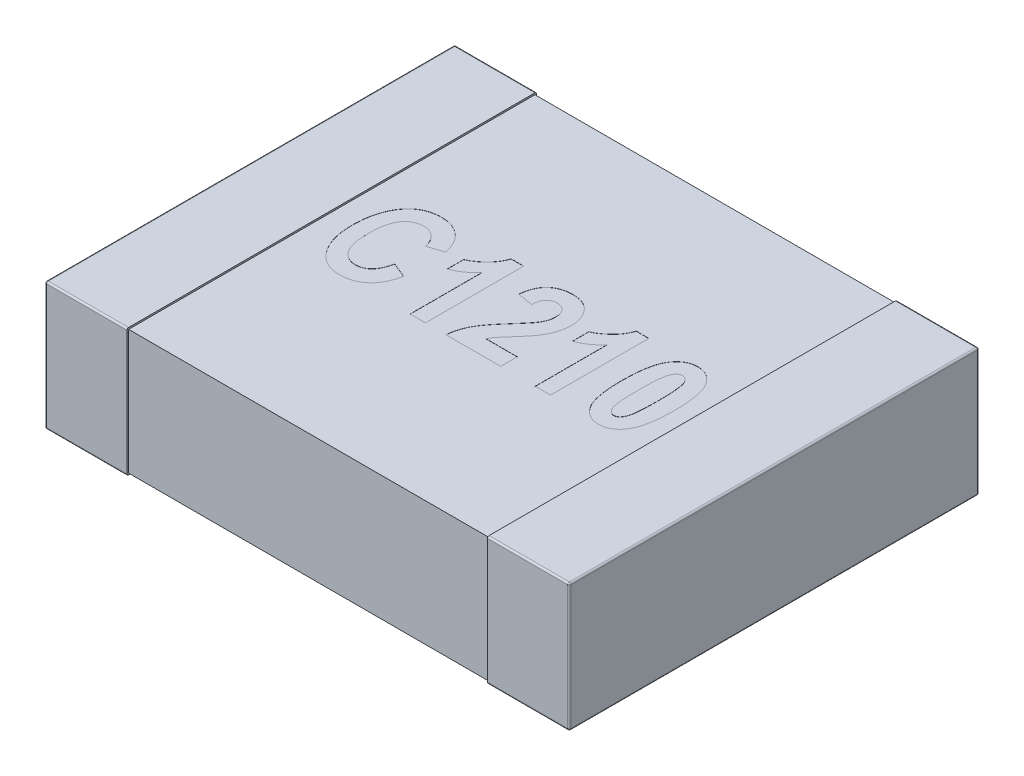
SolidWorks part; units mm, degrees
ref_plane "Front Plane" through (0, 0, 0) normal (0, 0, 1) x (1, 0, 0)
ref_plane "Top Plane" through (0, 0, 0) normal (0, 1, 0) x (1, 0, 0)
ref_plane "Right Plane" through (0, 0, 0) normal (1, 0, 0) x (0, 0, -1)
sketch "Sketch1" plane through (0, 0, 0) normal (0, 1, 0) x (1, 0, 0)
  line L0 (0, 0.15) -> (0, -0.15) construction
  line L1 (-1.6, 0) -> (0, 0) construction
  line L3 (-1.6, 1.25) -> (-1.1, 1.25)
  line L4 (-1.6, 1.25) -> (-1.6, -1.25)
  line L5 (-1.6, -1.25) -> (-1.1, -1.25)
  line L6 (-1.1, 1.25) -> (-1.1, -1.25)
  dimension "BANDWIDTH" = 0.5
  dimension "WIDTH" = 2.5
  dimension "LENGTH-HALF" = 1.6
extrude "THICKNESS" add sketch "Sketch1" along normal blind 0.78
fillet "Fillet1" radius 0.01 8 edges at (-1.6, 0, 0) (-1.35, 0, -1.25) (-1.6, 0.39, -1.25) (-1.35, 0, 1.25) (-1.6, 0.39, 1.25) (-1.6, 0.78, 0) (-1.35, 0.78, -1.25) (-1.35, 0.78, 1.25)
sketch "Sketch2" plane through (0, 0, 0) normal (1, 0, 0) x (0, 0, -1)
  line L0 (0, 0.78) -> (0, 0) construction
  line L1 (-1.24, 0.77) -> (1.24, 0.77)
  line L2 (-1.24, 0.77) -> (-1.24, 0.01)
  line L3 (-1.24, 0.01) -> (1.24, 0.01)
  line L4 (1.24, 0.77) -> (1.24, 0.01)
  line L5 (-1.24, 0.78) -> (1.24, 0.78) construction
  line L6 (-1.24, 0) -> (1.24, 0) construction
  line L7 (-1.25, 0.39) -> (1.25, 0.39) construction
  line L8 (-1.25, 0.77) -> (-1.25, 0.01) construction
  line L9 (1.25, 0.77) -> (1.25, 0.01) construction
  dimension "D1" = 0.01
  dimension "D2" = 0.01
extrude "Boss-Extrude2" add sketch "Sketch2" against normal up to surface (1.1 mm away) up to face at (-1.1, 0.39, 0)
mirror "Mirror3" about plane through (0, 0, 0) normal (1, 0, 0) of "Boss-Extrude2", "Fillet1", "THICKNESS"
sketch "Sketch3" plane through (0, 0.77, 0) normal (0, 1, 0) x (1, 0, 0)
  line L0 (-1, -0.3) -> (1, -0.3) construction
  line L1 (0, -0.429) -> (0, 0.429) construction
  line L2 (-0.429, 0) -> (0.429, 0) construction
  text T0 "<b>C1210</b>" font "Arial Narrow" height 0.6
  point P2 (0, -0.3)
  dimension "D1" = 2
  dimension "D2" = 0.3
extrude "Cut-Extrude1" cut sketch "Sketch3" against normal blind 0.001
